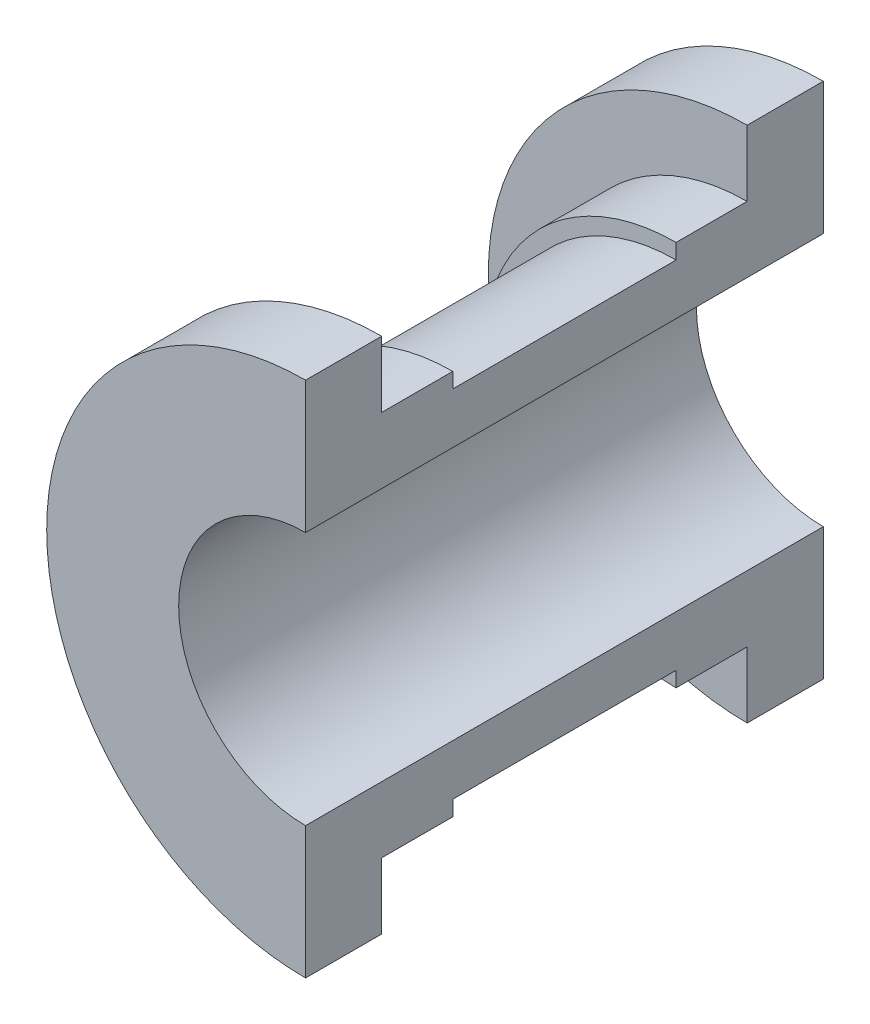
SolidWorks part; units mm, degrees
ref_plane "Front Plane" through (0, 0, 0) normal (0, 0, 1) x (1, 0, 0)
ref_plane "Top Plane" through (0, 0, 0) normal (0, 1, 0) x (1, 0, 0)
ref_plane "Right Plane" through (0, 0, 0) normal (1, 0, 0) x (0, 0, -1)
sketch "Sketch1" plane through (0, 0, 0) normal (0, 1, 0) x (1, 0, 0)
  line L1 (-12.5, 0) -> (-12.5, -51)
  line L2 (0, 45.6569) -> (0, -55.8366) construction
  line L3 (-12.5, -51) -> (-25.5, -51)
  line L4 (-25.5, -51) -> (-25.5, -43.5)
  line L5 (-25.5, -43.5) -> (-19, -43.5)
  line L6 (-19, -43.5) -> (-19, -36.5)
  line L7 (-19, -36.5) -> (-17.5, -36.5)
  line L8 (-17.5, -36.5) -> (-17.5, -14.5)
  line L9 (-17.5, -14.5) -> (-19, -14.5)
  line L10 (-19, -14.5) -> (-19, -7.5)
  line L11 (-19, -7.5) -> (-25.5, -7.5)
  line L12 (-25.5, -7.5) -> (-25.5, 0)
  line L13 (-25.5, 0) -> (-12.5, 0)
  dimension "D1" = 51
  dimension "D2" = 36
  dimension "D3" = 22
  dimension "D4" = 12.5
  dimension "D5" = 17.5
  dimension "D6" = 19
  dimension "D7" = 25.5
revolve "Revolve1" add sketch "Sketch1" angle 180 mid plane about L2
ref_plane "Plane1" through (-17.5, 0, 0) normal (1, 0, 0) x (0, 0, -1)
sketch "Sketch2" plane through (-17.5, 0, 0) normal (1, 0, 0) x (0, 0, -1)
  circle A0 centre (-25.5, 0) radius 3
  dimension "D1" = 25.5
  dimension "D2" = 6
extrude "Boss-Extrude1" add sketch "Sketch2" against normal blind 6 separate body
